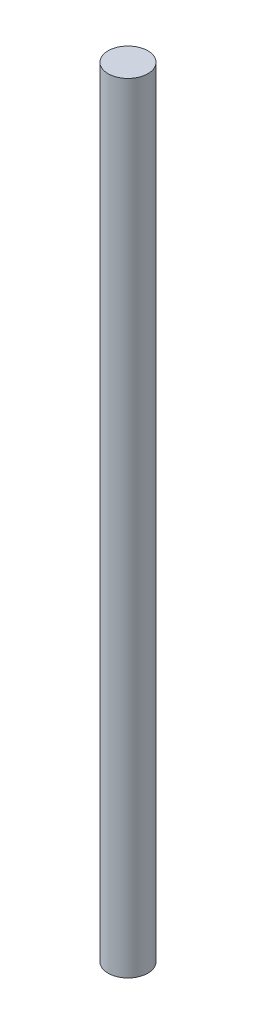
SolidWorks part; units mm, degrees
ref_plane "Front Plane" through (0, 0, 0) normal (0, 0, 1) x (1, 0, 0)
ref_plane "Top Plane" through (0, 0, 0) normal (0, 1, 0) x (1, 0, 0)
ref_plane "Right Plane" through (0, 0, 0) normal (1, 0, 0) x (0, 0, -1)
sketch "Sketch1" plane through (0, 0, 0) normal (0, 1, 0) x (1, 0, 0)
  circle A0 centre (0, 0) radius 2.5
  dimension "D1" = 5
extrude "Boss-Extrude1" add sketch "Sketch1" along normal blind 28 and the other way blind 70
